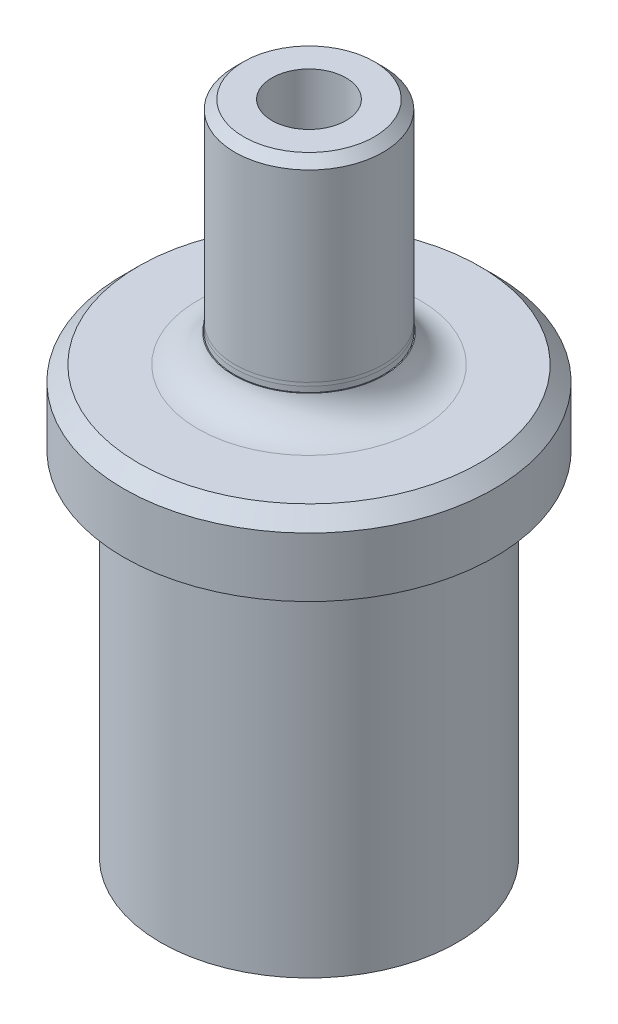
SolidWorks part; units mm, degrees
material "6061 Alloy"
ref_plane "Front Plane" through (0, 0, 0) normal (0, 0, 1) x (1, 0, 0)
ref_plane "Top Plane" through (0, 0, 0) normal (0, 1, 0) x (1, 0, 0)
ref_plane "Right Plane" through (0, 0, 0) normal (1, 0, 0) x (0, 0, -1)
sketch "Sketch1" plane through (0, 0, 0) normal (0, 1, 0) x (1, 0, 0)
  circle A0 centre (0, 0) radius 12.7
  dimension "D1" = 25.4
extrude "Boss-Extrude1" add sketch "Sketch1" along normal blind 30.1625
sketch "Sketch4" plane through (0, 30.1625, 0) normal (0, 1, 0) x (1, 0, 0)
  circle A0 centre (0, 0) radius 15.875
  dimension "D1" = 31.75
extrude "Boss-Extrude2" add sketch "Sketch4" along normal blind 50.8 contours A0
sketch "Sketch2" plane through (0, 0, 0) normal (0, -1, 0) x (1, 0, 0)
  line L0 (-8.777, 1.1225) -> (-1.1225, 8.777)
  line L1 (-5.4125, -7) -> (5.4125, -7)
  line L2 (-7, -5.4125) -> (-7, 5.4125)
  line L3 (-5.4125, 7) -> (5.4125, 7)
  line L4 (7, -5.4125) -> (7, 5.4125)
  line L5 (-7, -7) -> (7, 7) construction
  line L6 (-7, 7) -> (7, -7) construction
  line L7 (-8.777, -1.1225) -> (-1.1225, -8.777)
  line L8 (1.1225, 8.777) -> (8.777, 1.1225)
  line L9 (1.1225, -8.777) -> (8.777, -1.1225)
  line L10 (-9.8995, 0) -> (9.8995, 0) construction
  line L11 (0, 9.8995) -> (0, -9.8995) construction
  circle A0 centre (0, 0) radius 9 construction
  arc A1 (-8.777, 1.1225) -> (-8.777, -1.1225) centre (-7.6544, 0) ccw
  arc A2 (-7, -5.4125) -> (-5.4125, -7) centre (-5.4125, -5.4125) ccw
  arc A3 (-1.1225, -8.777) -> (1.1225, -8.777) centre (0, -7.6544) ccw
  arc A4 (5.4125, -7) -> (7, -5.4125) centre (5.4125, -5.4125) ccw
  arc A5 (8.777, -1.1225) -> (8.777, 1.1225) centre (7.6544, 0) ccw
  arc A6 (7, 5.4125) -> (5.4125, 7) centre (5.4125, 5.4125) ccw
  arc A7 (1.1225, 8.777) -> (-1.1225, 8.777) centre (0, 7.6544) ccw
  arc A8 (-5.4125, 7) -> (-7, 5.4125) centre (-5.4125, 5.4125) ccw
  point P0 (0, 0)
  point P7 (0, 0)
  dimension "D2" = 18
  dimension "D3" = 1.5875
  dimension "D1" = 14
extrude "Cut-Extrude1" cut sketch "Sketch2" against normal blind 11.176 contours L0 A1 L7 L2 | L1 L9 L4 L8 L3 L0 L2 L7 | L3 A8 L2 L0 | L8 A7 L0 L3 | L4 A6 L3 L8 | L9 A5 L8 L4 | L1 A4 L4 L9 | L7 A3 L9 L1 | L2 A2 L1 L7
sketch "Sketch3" plane through (0, 11.176, 0) normal (0, -1, 0) x (1, 0, 0)
  circle A0 centre (0, 0) radius 6
  dimension "D1" = 12
extrude "Cut-Extrude2" cut sketch "Sketch3" against normal blind 8
sketch "Sketch5" plane through (0, 80.9625, 0) normal (0, 1, 0) x (1, 0, 0)
  circle A0 centre (0, 0) radius 3.175
  dimension "D1" = 6.35
extrude "Boss-Extrude3" add sketch "Sketch5" along normal blind 6.604
hole_wizard "#8-32 Tapped Hole1" positions "Sketch6" profile "Sketch8" tap size "#8-32" standard "ANSI Inch" end condition through all
sketch "Sketch6" plane through (0, 87.5665, 0) normal (0, 1, 0) x (1, 0, 0)
  point P0 (0, 0)
sketch "Sketch8" plane through (0, 87.5665, 0) normal (1, 0, 0) x (0, 0, 1)
  line L0 (0, 0) -> (0, 87.5665)
  line L1 (0, 87.5665) -> (1.7272, 87.5665)
  line L2 (1.7272, 87.5665) -> (1.7272, 0)
  line L5 (1.7272, 0) -> (0, 0)
  line L11 (0, -6.35) -> (0, 107.95) construction
  dimension "Thru Tap Drill Dia." = 3.4544
  dimension "Thru Tap Drill Depth" = 87.5665
cosmetic thread "Hole Thread1" [suppressed] parameters "D2"=4.1656
sketch "Sketch9" plane through (0, 80.9625, 0) normal (0, 1, 0) x (1, 0, 0)
  circle A0 centre (0, 0) radius 15.875 construction
  circle A1 centre (0, 0) radius 15.875
  circle A2 centre (0, 0) radius 6.35
  dimension "D1" = 12.7
extrude "Cut-Extrude3" cut sketch "Sketch9" against normal blind 38.1 from offset 6.35 offset against normal yes
fillet "Fillet1" radius 3.175 2 edges at (0, 74.6125, 6.35) (0, 36.5125, 6.35)
chamfer "Chamfer1" distance 1.27 angle 45 1 edges at (0, 36.5125, 15.875)
sketch "Sketch10" plane through (0, 0, 0) normal (0, 0, 1) x (1, 0, 0)
  line L0 (0, 87.5665) -> (0, 56.1975)
  line L1 (1.7272, 87.5665) -> (-1.7272, 87.5665) construction
  line L2 (0, 56.1975) -> (-6.3627, 56.1975)
  line L4 (-6.3627, 56.1975) -> (-6.3627, 38.9382)
  line L5 (-6.3627, 38.9382) -> (-15.875, 38.9382)
  line L6 (-15.875, 38.9382) -> (-15.875, 87.5665)
  line L7 (-15.875, 87.5665) -> (0, 87.5665)
  line L8 (-15.875, 80.9625) -> (-15.875, 74.6125) construction
  line L9 (-12.7, 0) -> (12.7, 0) construction
  line L10 (-15.875, 38.9382) -> (-15.875, 30.1625)
  line L11 (-15.875, 30.1625) -> (-12.7, 30.1625)
  line L12 (-12.7, 30.1625) -> (-12.7, 38.9382)
  dimension "D1" = 38.9382
  dimension "D2" = 56.1975
  dimension "D3" = 12.7
  dimension "D4" = 6.3627
revolve "Cut-Revolve1" cut sketch "Sketch10" angle 360 about L0
hole_wizard "1/4 (0.25) Diameter Hole1" positions "Sketch11" profile "Sketch13" hole size "1/4" standard "ANSI Inch"
sketch "Sketch11" plane through (0, 56.1975, 0) normal (0, 1, 0) x (1, 0, 0)
  point P0 (0, 0)
sketch "Sketch13" plane through (0, 56.1975, 0) normal (1, 0, 0) x (0, 0, 1)
  line L0 (0, 0) -> (0, 8.2577)
  line L1 (0, 8.2577) -> (3.175, 6.35)
  line L2 (3.175, 6.35) -> (3.175, 0)
  line L5 (3.175, 0) -> (0, 0)
  line L10 (0, 8.2577) -> (-3.175, 6.35) construction
  line L11 (0, -6.35) -> (0, 107.95) construction
  dimension "Hole Dia." = 6.35
  dimension "Hole Depth" = 6.35
  dimension "Drill Angle" = 118
chamfer "Chamfer2" distance 0.762 angle 45 1 edges at (-6.35, 56.1975, 0)
equation "\"D4@Sketch10\"=.5/2+.0005"
